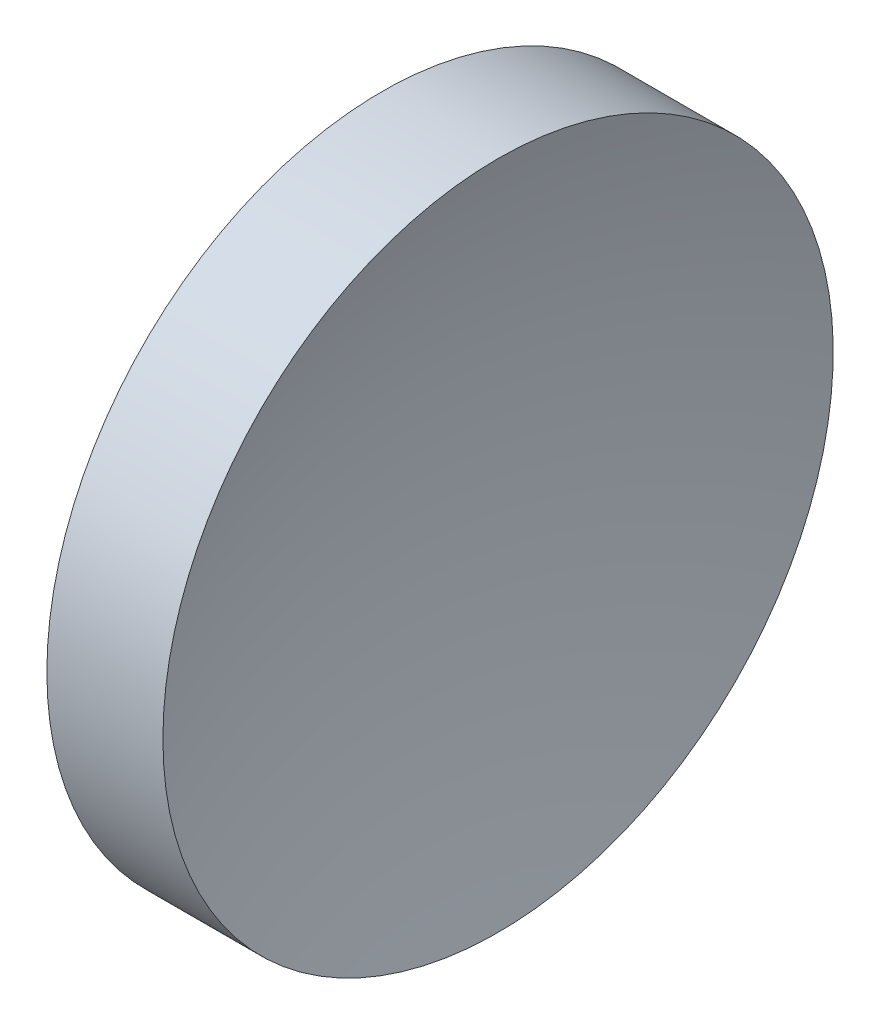
SolidWorks part; units mm, degrees
ref_plane "前视基准面" through (0, 0, 0) normal (0, 0, 1) x (1, 0, 0)
ref_plane "上视基准面" through (0, 0, 0) normal (0, 1, 0) x (1, 0, 0)
ref_plane "右视基准面" through (0, 0, 0) normal (1, 0, 0) x (0, 0, -1)
sketch "草图1" plane through (0, 0, 0) normal (0, 0, 1) x (1, 0, 0)
  line L0 (42.4499, 26.089) -> (50.324, 26.089) construction
  line L1 (44.3192, 26.089) -> (44.3192, 34.089)
  line L2 (45.8192, 26.089) -> (44.3192, 26.089)
  line L3 (44.3192, 34.089) -> (47.0887, 34.089)
  arc A0 (47.0887, 34.089) -> (45.8192, 26.089) centre (71.6592, 26.089) ccw
  dimension "D3" = 25.84
  dimension "D1" = 8
  dimension "D2" = 2.7696
revolve "旋转1" add sketch "草图1" angle 360 about L0
